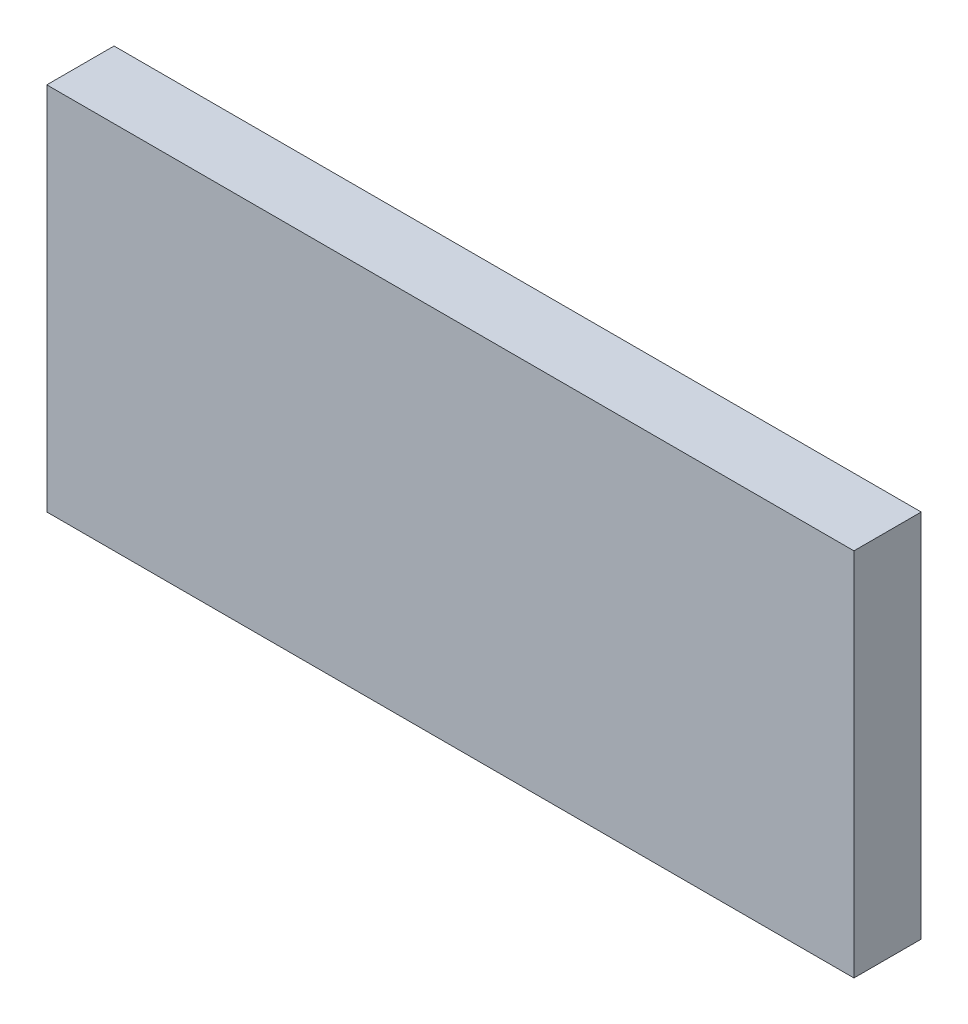
SolidWorks part; units mm, degrees
ref_plane "前基準面" through (0, 0, 0) normal (0, 0, 1) x (1, 0, 0)
ref_plane "上基準面" through (0, 0, 0) normal (0, 1, 0) x (1, 0, 0)
ref_plane "右基準面" through (0, 0, 0) normal (1, 0, 0) x (0, 0, -1)
sketch "草圖1" plane through (0, 0, 0) normal (0, 0, 1) x (1, 0, 0)
  line L0 (55, 0) -> (-55, 0) construction
  line L1 (-60, 27.5) -> (60, 27.5)
  line L2 (-60, 27.5) -> (-60, -27.5)
  line L3 (-60, -27.5) -> (60, -27.5)
  line L4 (60, 27.5) -> (60, -27.5)
  line L5 (0, -55) -> (0, 55) construction
  dimension "D1" = 120
  dimension "D2" = 55
  dimension "D3" = 27.5
  dimension "D4" = 60
extrude "填料-伸長1" add sketch "草圖1" along normal blind 10
